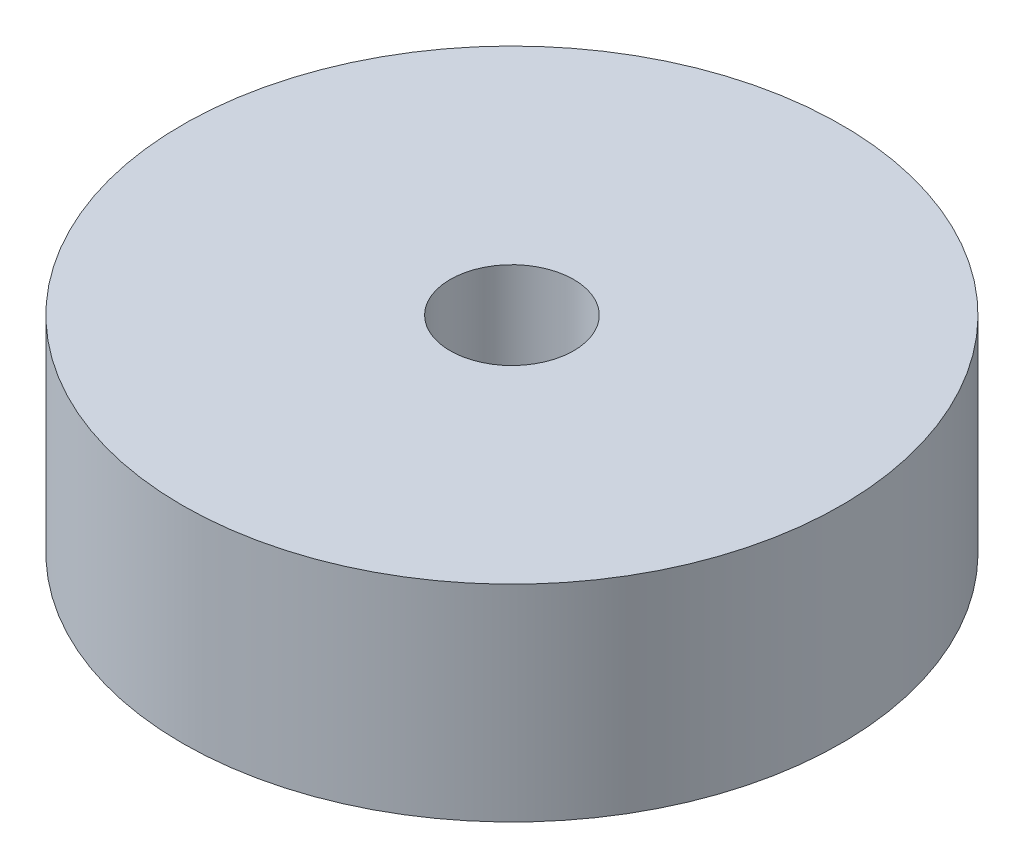
SolidWorks part; units mm, degrees
material "1023 Carbon Steel Sheet (SS)"
ref_plane "Front Plane" through (0, 0, 0) normal (0, 0, 1) x (1, 0, 0)
ref_plane "Top Plane" through (0, 0, 0) normal (0, 1, 0) x (1, 0, 0)
ref_plane "Right Plane" through (0, 0, 0) normal (1, 0, 0) x (0, 0, -1)
sketch "Sketch1" plane through (0, 0, 0) normal (0, 0, 1) x (1, 0, 0)
  line L0 (0, 41.306) -> (0, -42.6753) construction
  line L1 (0, 22.225) -> (1.27, 22.225)
  line L2 (1.27, 22.225) -> (1.27, 25.4)
  line L3 (1.27, 25.4) -> (25.4, 25.4)
  line L4 (25.4, 25.4) -> (25.4, 9.525)
  line L5 (25.4, 9.525) -> (9.525, 9.525)
  line L6 (9.525, 9.525) -> (9.525, 0)
  line L7 (9.525, 0) -> (0, 0)
  line L8 (0, 0) -> (0, 22.225)
  dimension "D1" = 9.525
  dimension "D2" = 25.4
  dimension "D3" = 15.875
  dimension "D4" = 9.525
  dimension "D5" = 3.175
  dimension "D6" = 1.27
  dimension "D7" = 24.13
  dimension "D8" = 0
revolve "Revolve2" add sketch "Sketch1" angle 360 about L0
sketch "Sketch2" plane through (0, 0, 0) normal (0, -1, 0) x (1, 0, 0)
  circle A0 centre (0, 0) radius 4.7625
  dimension "D1" = 9.525
extrude "Cut-Extrude1" cut sketch "Sketch2" against normal blind 28.702
